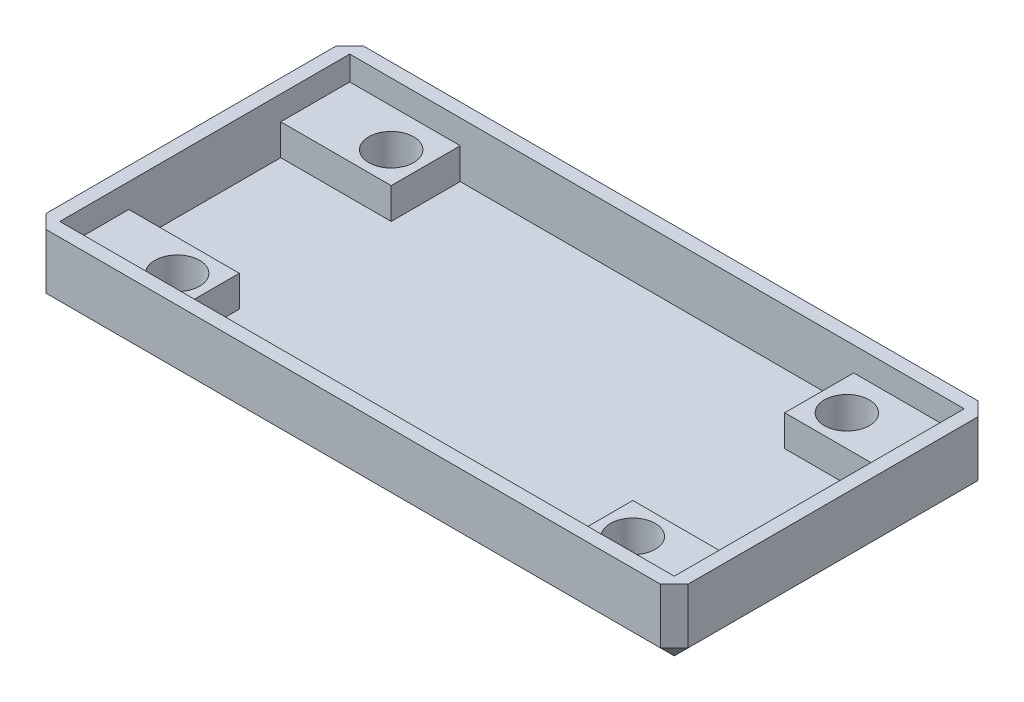
SolidWorks part; units mm, degrees
ref_plane "Front Plane" through (0, 0, 0) normal (0, 0, 1) x (1, 0, 0)
ref_plane "Top Plane" through (0, 0, 0) normal (0, 1, 0) x (1, 0, 0)
ref_plane "Right Plane" through (0, 0, 0) normal (1, 0, 0) x (0, 0, -1)
sketch "Sketch1" plane through (0, 0, 0) normal (0, 1, 0) x (1, 0, 0)
  line L1 (-23.25, -11.5) -> (23.25, -11.5)
  line L2 (-23.25, -11.5) -> (-23.25, 11.5)
  line L3 (-23.25, 11.5) -> (23.25, 11.5)
  line L4 (23.25, -11.5) -> (23.25, 11.5)
  line L5 (-23.25, -11.5) -> (23.25, 11.5) construction
  line L6 (-23.25, 11.5) -> (23.25, -11.5) construction
  point P0 (0, 0)
  dimension "D1" = 46.5
  dimension "D2" = 23
extrude "Boss-Extrude1" add sketch "Sketch1" along normal blind 5
sketch "Sketch2" plane through (0, 5, 0) normal (0, 1, 0) x (1, 0, 0)
  line L1 (-22.25, -10.5) -> (22.25, -10.5)
  line L2 (-22.25, -10.5) -> (-22.25, 10.5)
  line L3 (-22.25, 10.5) -> (22.25, 10.5)
  line L4 (22.25, -10.5) -> (22.25, 10.5)
  line L5 (-22.25, -10.5) -> (22.25, 10.5) construction
  line L6 (-22.25, 10.5) -> (22.25, -10.5) construction
  point P0 (0, 0)
  dimension "D1" = 44.5
  dimension "D2" = 21
extrude "Cut-Extrude1" cut sketch "Sketch2" against normal blind 4
sketch "Sketch3" plane through (0, 1, 0) normal (0, 1, 0) x (1, 0, 0)
  line L0 (0, -55) -> (0, 55) construction
  line L1 (-22.25, 10.5) -> (-14.25, 10.5)
  line L2 (-22.25, 10.5) -> (-22.25, 5.5)
  line L3 (-22.25, 5.5) -> (-14.25, 5.5)
  line L4 (-14.25, 10.5) -> (-14.25, 5.5)
  line L5 (14.25, 10.5) -> (14.25, 5.5)
  line L6 (22.25, 5.5) -> (14.25, 5.5)
  line L7 (22.25, 10.5) -> (22.25, 5.5)
  line L8 (22.25, 10.5) -> (14.25, 10.5)
  line L9 (-55, 0) -> (55, 0) construction
  line L10 (22.25, -10.5) -> (14.25, -10.5)
  line L11 (22.25, -10.5) -> (22.25, -5.5)
  line L12 (22.25, -5.5) -> (14.25, -5.5)
  line L13 (14.25, -10.5) -> (14.25, -5.5)
  line L14 (-14.25, -10.5) -> (-14.25, -5.5)
  line L15 (-22.25, -5.5) -> (-14.25, -5.5)
  line L16 (-22.25, -10.5) -> (-22.25, -5.5)
  line L17 (-22.25, -10.5) -> (-14.25, -10.5)
  dimension "D1" = 8
  dimension "D2" = 5
extrude "Boss-Extrude2" add sketch "Sketch3" along normal blind 2.25
sketch "Sketch4" plane through (0, 3.25, 0) normal (0, 1, 0) x (1, 0, 0)
  line L2 (0, -2.75) -> (0, 2.75) construction
  line L3 (-2.75, 0) -> (2.75, 0) construction
  line L5 (22, -10.25) -> (-22, -10.25) construction
  line L6 (22, -10.25) -> (22, 10.25) construction
  line L7 (22, 10.25) -> (-22, 10.25) construction
  line L8 (-22, -10.25) -> (-22, 10.25) construction
  line L9 (22, -10.25) -> (-22, 10.25) construction
  line L10 (22, 10.25) -> (-22, -10.25) construction
  circle A0 centre (-16.5, 7.75) radius 1.625
  circle A1 centre (16.5, 7.75) radius 1.625
  circle A2 centre (16.5, -7.75) radius 1.625
  circle A3 centre (-16.5, -7.75) radius 1.625
  point P18 (0, 0)
  dimension "D1" = 3.25
  dimension "D2" = 2.5
  dimension "D3" = 5.5
  dimension "D4" = 44
  dimension "D5" = 20.5
extrude "Cut-Extrude2" cut sketch "Sketch4" against normal through all
chamfer "Chamfer1" distance 1 angle 45 8 edges at (0, 0, -11.5) (-23.25, 2.5, -11.5) (-23.25, 0, 0) (23.25, 2.5, -11.5) (23.25, 0, 0) (23.25, 2.5, 11.5) (0, 0, 11.5) (-23.25, 2.5, 11.5)
